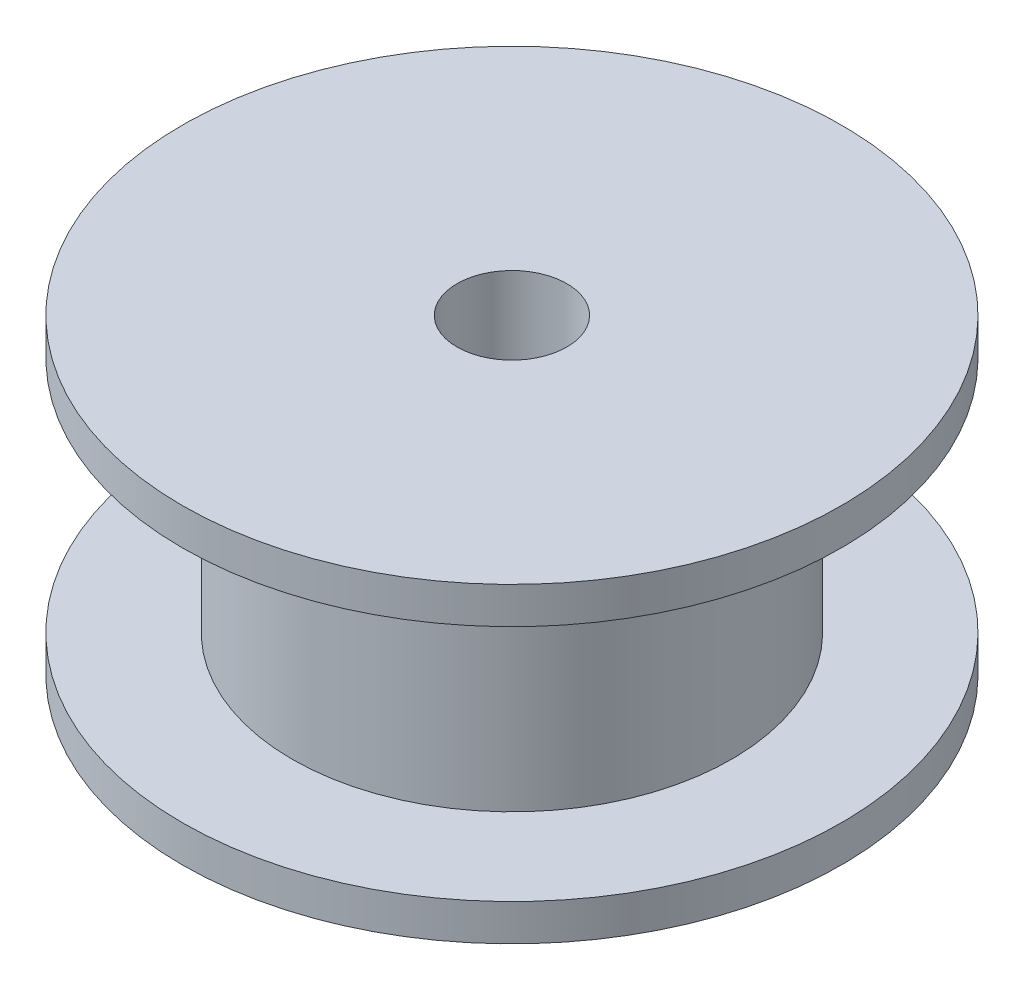
SolidWorks part; units mm, degrees
ref_plane "前视基准面" through (0, 0, 0) normal (0, 0, 1) x (1, 0, 0)
ref_plane "上视基准面" through (0, 0, 0) normal (0, 1, 0) x (1, 0, 0)
ref_plane "右视基准面" through (0, 0, 0) normal (1, 0, 0) x (0, 0, -1)
sketch "草图1" plane through (0, 0, 0) normal (0, 1, 0) x (1, 0, 0)
  circle A0 centre (0, 0) radius 9
  dimension "D1" = 18
extrude "凸台-拉伸1" add sketch "草图1" along normal blind 1
sketch "草图2" plane through (0, 1, 0) normal (0, 1, 0) x (1, 0, 0)
  circle A0 centre (0, 0) radius 6
  dimension "D1" = 12
extrude "凸台-拉伸2" add sketch "草图2" along normal blind 6.5
sketch "草图3" plane through (0, 7.5, 0) normal (0, 1, 0) x (1, 0, 0)
  circle A0 centre (0, 0) radius 9
  dimension "D1" = 18
extrude "凸台-拉伸3" add sketch "草图3" along normal blind 1
sketch "草图4" plane through (0, 8.5, 0) normal (0, 1, 0) x (1, 0, 0)
  circle A0 centre (0, 0) radius 1.5
  dimension "D1" = 3
extrude "切除-拉伸1" cut sketch "草图4" against normal through all
